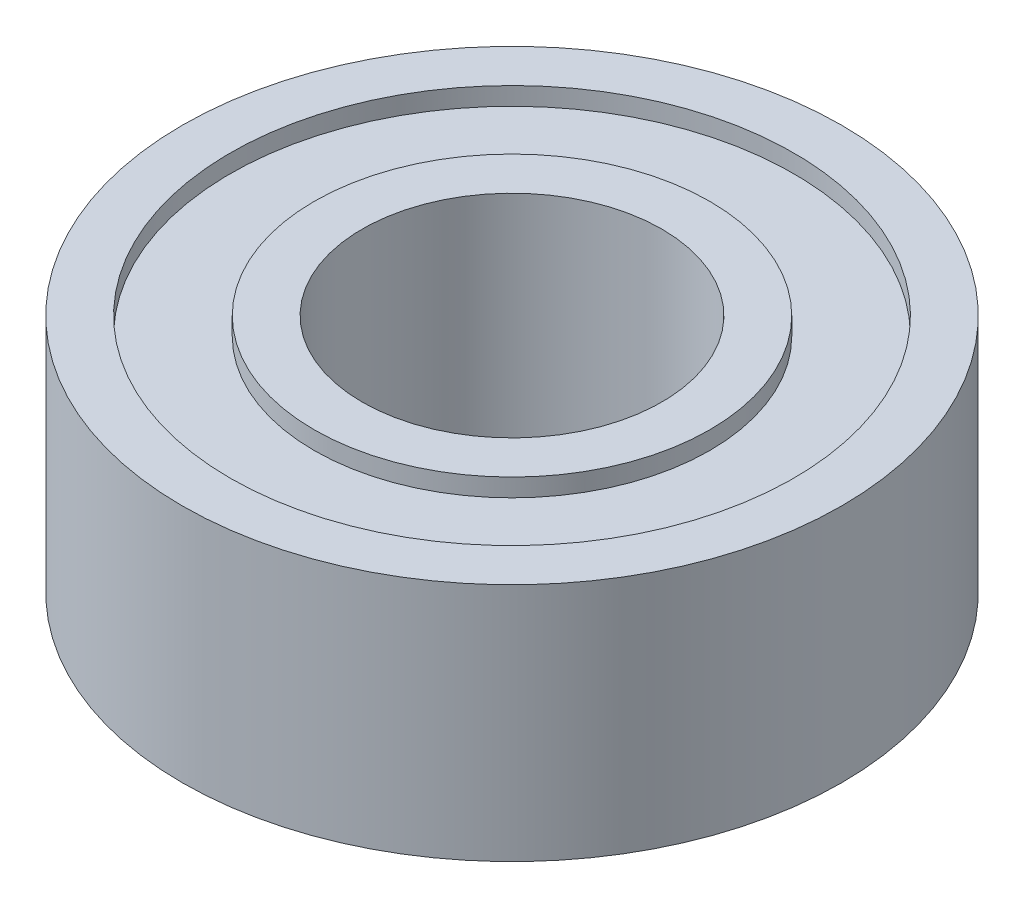
SolidWorks part; units mm, degrees
ref_plane "Plan de face" through (0, 0, 0) normal (0, 0, 1) x (1, 0, 0)
ref_plane "Plan de dessus" through (0, 0, 0) normal (0, 1, 0) x (1, 0, 0)
ref_plane "Plan de droite" through (0, 0, 0) normal (1, 0, 0) x (0, 0, -1)
sketch "Esquisse1" plane through (0, 0, 0) normal (0, 0, 1) x (1, 0, 0)
  line L0 (0, 4.5345) -> (0, -3.5944) construction
  line L1 (-8.0597, 0) -> (11.1022, 0) construction
  line L2 (2.5, -2) -> (2.5, 2)
  line L3 (2.5, 2) -> (3.3, 2)
  line L4 (3.3, 2) -> (3.3, 1.7)
  line L5 (3.3, 1.7) -> (4.7, 1.7)
  line L6 (4.7, 1.7) -> (4.7, 2)
  line L7 (4.7, 2) -> (5.5, 2)
  line L8 (5.5, 2) -> (5.5, -2)
  line L9 (4.7, -2) -> (5.5, -2)
  line L10 (4.7, -1.7) -> (4.7, -2)
  line L11 (3.3, -1.7) -> (4.7, -1.7)
  line L12 (3.3, -2) -> (3.3, -1.7)
  line L13 (2.5, -2) -> (3.3, -2)
  point P14 (5.5, 0)
  point P19 (2.5, 0)
  dimension "D1" = 0.8
  dimension "D2" = 0.8
  dimension "D3" = 3
  dimension "D4" = 2
  dimension "D5" = 2
  dimension "D6" = 0.3
  dimension "D7" = 5.5
revolve "Révolution1" add sketch "Esquisse1" angle 360 about L0
